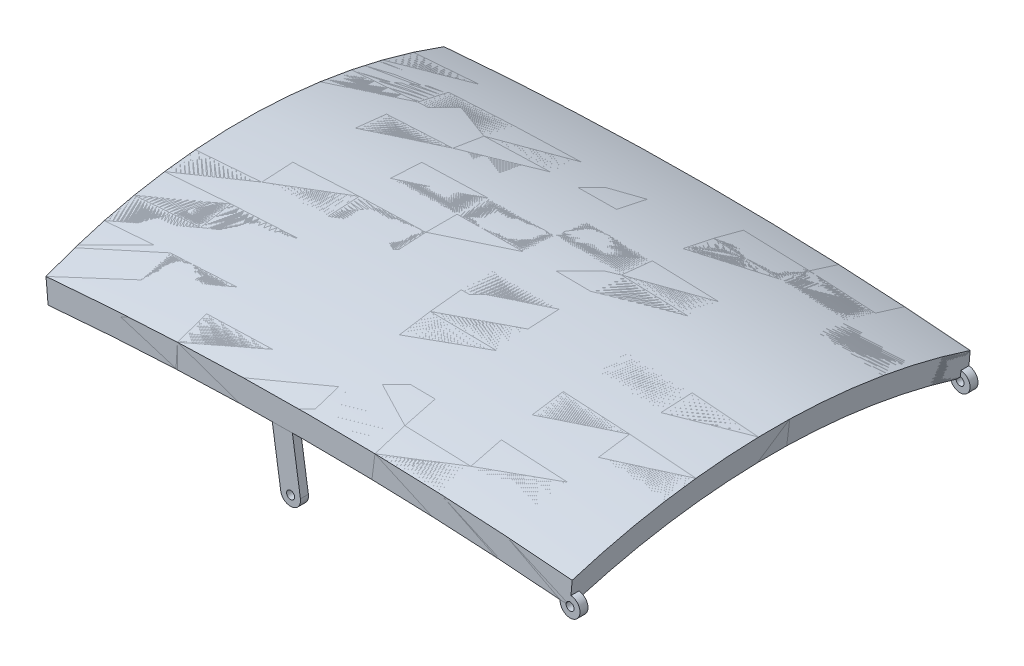
SolidWorks part; units mm, degrees
material "Alloy Steel"
ref_plane "Front Plane" through (0, 0, 0) normal (0, 0, 1) x (1, 0, 0)
ref_plane "Top Plane" through (0, 0, 0) normal (0, 1, 0) x (1, 0, 0)
ref_plane "Right Plane" through (0, 0, 0) normal (1, 0, 0) x (0, 0, -1)
sketch "Sketch1" plane through (0, 0, 0) normal (0, 0, 1) x (1, 0, 0)
  arc A0 (-381.3463, 0) -> (930.2537, 0) centre (274.4537, -7406.5232) cw
  dimension "D2" = 7435.5
  dimension "D1" = 1311.6
ref_plane "Plane1" through (-381.3463, 0, 0) normal (0.9961, 0.0882, 0) x (0, 0, -1)
sketch "Sketch2" plane through (-381.3463, 0, 0) normal (0.9961, 0.0882, 0) x (0, 0, -1)
  line L2 (1000, 0) -> (1000, 60)
  line L4 (0, 0) -> (0, 60)
  arc A0 (1000, 60) -> (0, 60) centre (500, -1354.2136) ccw
  arc A1 (1000, 0) -> (0, 0) centre (500, -1414.2136) ccw
  point P0 (0, 0)
  dimension "D3" = 1500
  dimension "D5" = 60
  dimension "D1" = 60
  dimension "D2" = 1000
  dimension "D4" = 60
sweep "Sweep1" add profiles "Sketch2" path "Sketch1"
sketch "Sketch3" plane through (0, 0, 0) normal (0, 0, 1) x (1, 0, 0)
  line L0 (-381.3463, 0) -> (930.2537, 0) construction
  line L1 (207.1537, 28.6722) -> (227.9709, -108.3278)
  line L2 (203.2546, -112.0835) -> (181.908, 28.4008)
  line L3 (252.6872, -104.5722) -> (232.4125, 28.8579)
  line L5 (179.8889, 41.689) -> (230.4628, 41.689)
  line L6 (232.4125, 28.8579) -> (230.4628, 41.689)
  line L7 (207.1537, 28.6722) -> (205.1758, 41.689)
  line L8 (181.908, 28.4008) -> (179.8889, 41.689)
  arc A0 (930.2537, 0) -> (-381.3463, 0) centre (274.4537, -7406.5232) ccw construction
  circle A1 centre (227.9709, -108.3278) radius 10
  circle A2 centre (227.9709, -108.3278) radius 25
  dimension "D4" = 20
  dimension "D5" = 50
  dimension "D1" = 81.36
  dimension "D2" = 137
  dimension "D3" = 723.1
extrude "Boss-Extrude1" add sketch "Sketch3" against normal blind 20 separate body
sketch "Sketch4" plane through (0, 0, 0) normal (0, 0, 1) x (1, 0, 0)
  circle A1 centre (930.2537, 0) radius 25
  dimension "D2" = 50
extrude "Boss-Extrude2" add sketch "Sketch4" against normal blind 20
sketch "Sketch5" plane through (0, 0, 0) normal (0, 0, 1) x (1, 0, 0)
  circle A0 centre (930.2537, 0) radius 10
  dimension "D1" = 20
extrude "Cut-Extrude1" cut sketch "Sketch5" against normal blind 40
sketch "Sketch8" plane through (-378.3798, -33.5031, 0) normal (-0.9961, -0.0882, 0) x (0, 0, 1)
  line L0 (0, 33.6342) -> (-1000, 33.6342)
ref_point "Point1"
ref_plane "Plane2" through (0, 0, -500) normal (0, 0, 1) x (1, 0, 0)
mirror "Mirror5" about plane through (0, 0, -500) normal (0, 0, 1) of bodies 102 104
sketch "Sketch9" plane through (0, 0, 0) normal (0, 0, 1) x (1, 0, 0)
  circle A0 centre (930.2537, 0) radius 10 construction
  circle A1 centre (930.2537, 0) radius 10
extrude "Cut-Extrude2" cut sketch "Sketch9" against normal through all both and the other way through all
